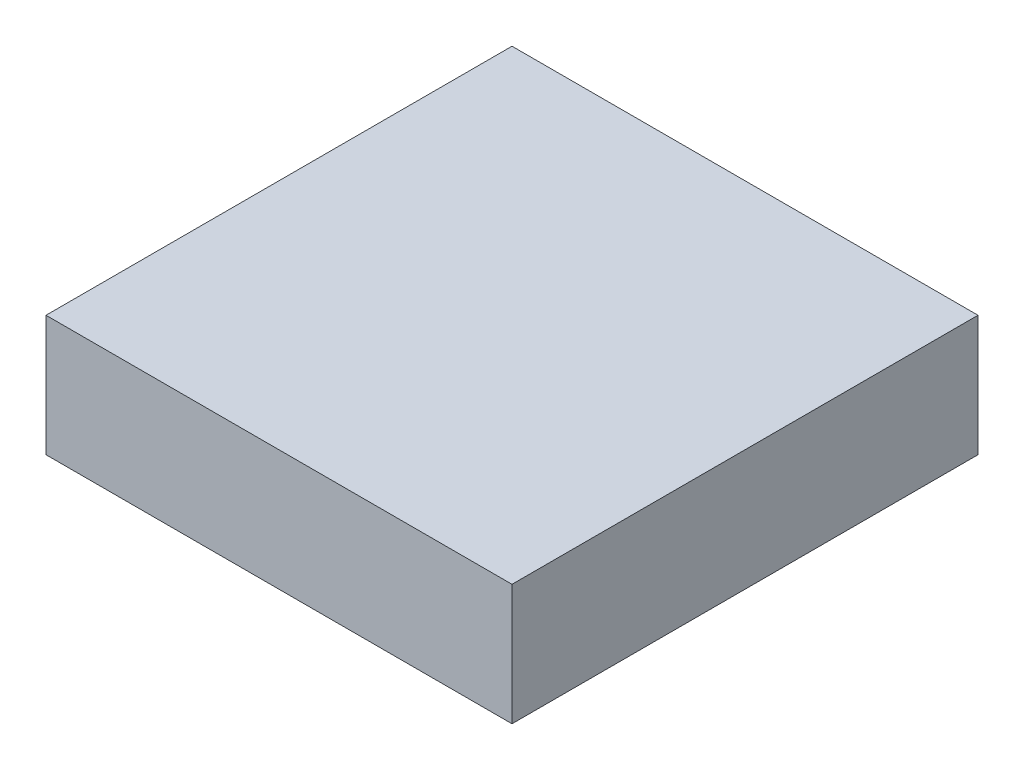
SolidWorks part; units mm, degrees
ref_plane "Front Plane" through (0, 0, 0) normal (0, 0, 1) x (1, 0, 0)
ref_plane "Top Plane" through (0, 0, 0) normal (0, 1, 0) x (1, 0, 0)
ref_plane "Right Plane" through (0, 0, 0) normal (1, 0, 0) x (0, 0, -1)
sketch "Sketch1" plane through (0, 0, 0) normal (0, 1, 0) x (1, 0, 0)
  line L1 (0, 0) -> (27, 0)
  line L2 (0, 0) -> (0, 27)
  line L3 (0, 27) -> (27, 27)
  line L4 (27, 0) -> (27, 27)
  dimension "D1" = 27
  dimension "D2" = 27
extrude "Boss-Extrude1" add sketch "Sketch1" along normal blind 7
